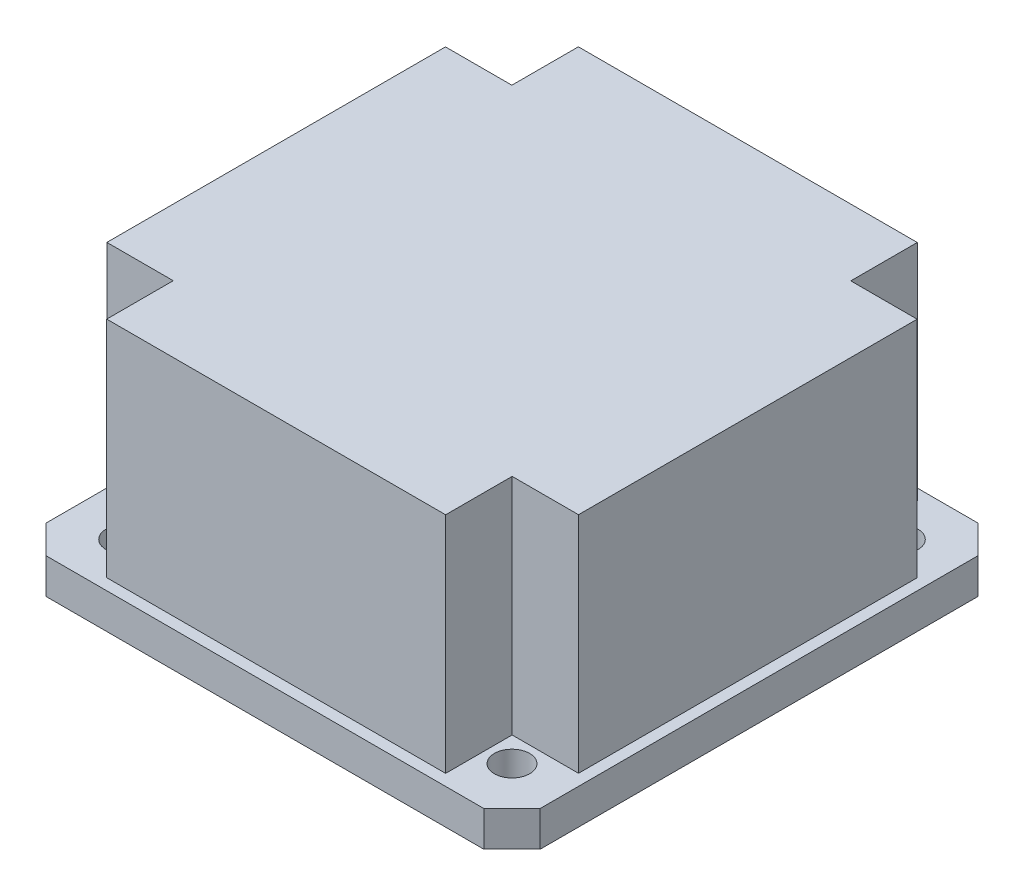
SolidWorks part; units mm, degrees
ref_plane "Front Plane" through (0, 0, 0) normal (0, 0, 1) x (1, 0, 0)
ref_plane "Top Plane" through (0, 0, 0) normal (0, 1, 0) x (1, 0, 0)
ref_plane "Right Plane" through (0, 0, 0) normal (1, 0, 0) x (0, 0, -1)
sketch "Sketch2" plane through (0, 0, 0) normal (0, 1, 0) x (1, 0, 0)
  line L1 (-22.225, -22.225) -> (22.225, -22.225)
  line L2 (-22.225, -22.225) -> (-22.225, 22.225)
  line L3 (-22.225, 22.225) -> (22.225, 22.225)
  line L4 (22.225, -22.225) -> (22.225, 22.225)
  line L5 (-22.225, -22.225) -> (22.225, 22.225) construction
  line L6 (-22.225, 22.225) -> (22.225, -22.225) construction
  point P0 (0, 0)
  dimension "D1" = 44.45
  dimension "D2" = 44.45
extrude "Boss-Extrude1" add sketch "Sketch2" along normal blind 3.175
chamfer "Chamfer1" distance 2.54 angle 45 4 edges at (22.225, 1.5875, -22.225) (22.225, 1.5875, 22.225) (-22.225, 1.5875, 22.225) (-22.225, 1.5875, -22.225)
sketch "Sketch3" plane through (0, 3.175, 0) normal (0, 1, 0) x (1, 0, 0)
  line L0 (0, 22.225) -> (0, -22.225) construction
  line L1 (19.685, 22.225) -> (-19.685, 22.225) construction
  line L2 (-19.685, -22.225) -> (19.685, -22.225) construction
  line L3 (-22.225, 0) -> (22.225, 0) construction
  line L4 (-22.225, 19.685) -> (-22.225, -19.685) construction
  line L5 (22.225, -19.685) -> (22.225, 19.685) construction
  circle A0 centre (-17.4625, 17.4625) radius 1.5875
  dimension "D3" = 3.175
  dimension "D1" = 34.925
  dimension "D2" = 34.925
extrude "Cut-Extrude1" cut sketch "Sketch3" against normal through all
mirror "Mirror1" about plane through (0, 0, 0) normal (1, 0, 0) of "Cut-Extrude1"
mirror "Mirror2" about plane through (0, 0, 0) normal (0, 0, 1) of "Mirror1", "Cut-Extrude1"
sketch "Sketch4" plane through (0, 3.175, 0) normal (0, 1, 0) x (1, 0, 0)
  line L1 (-21.209, -21.209) -> (21.209, -21.209)
  line L2 (-21.209, -21.209) -> (-21.209, 21.209)
  line L3 (-21.209, 21.209) -> (21.209, 21.209)
  line L4 (21.209, -21.209) -> (21.209, 21.209)
  line L5 (-21.209, -21.209) -> (21.209, 21.209) construction
  line L6 (-21.209, 21.209) -> (21.209, -21.209) construction
  point P0 (0, 0)
  dimension "D1" = 42.418
  dimension "D2" = 42.418
extrude "Boss-Extrude2" add sketch "Sketch4" along normal blind 20.1422
sketch "Sketch5" plane through (0, 23.3172, 0) normal (0, 1, 0) x (1, 0, 0)
  line L5 (-21.209, 21.209) -> (-15.24, 21.209)
  line L6 (-21.209, 21.209) -> (-21.209, 15.2273)
  line L7 (-21.209, 15.2273) -> (-15.24, 15.2273)
  line L8 (-15.24, 21.209) -> (-15.24, 15.2273)
  dimension "D1" = 5.969
  dimension "D2" = 5.9817
extrude "Cut-Extrude2" cut sketch "Sketch5" against normal up to surface (20.1422 mm away) up to face at (0, 3.175, -21.717)
mirror "Mirror3" about plane through (0, 0, 0) normal (1, 0, 0) of "Cut-Extrude2" second plane through (0, 0, 0) second plane normal (0, 0, 1)
